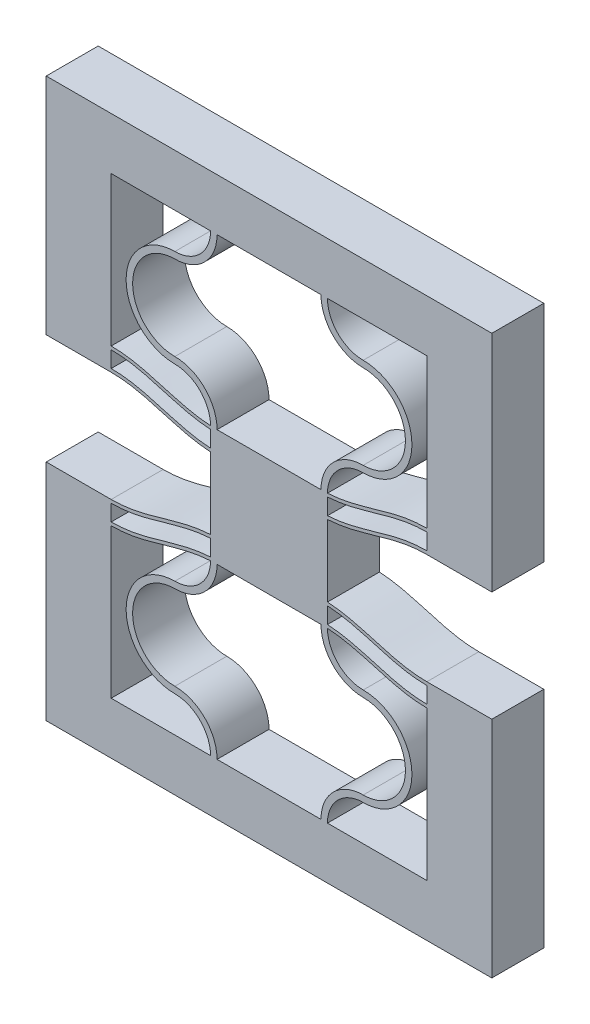
SolidWorks part; units mm, degrees
ref_plane "Front Plane" through (0, 0, 0) normal (0, 0, 1) x (1, 0, 0)
ref_plane "Top Plane" through (0, 0, 0) normal (0, 1, 0) x (1, 0, 0)
ref_plane "Right Plane" through (0, 0, 0) normal (1, 0, 0) x (0, 0, -1)
sketch "Sketch1" plane through (0, 0, 0) normal (0, 0, 1) x (1, 0, 0)
  line L4 (0, 11.5) -> (0, 0)
  line L5 (8.15, 0) -> (8.15, 13) construction
  line L6 (8.15, 13) -> (8.15, 15.9894) construction
  line L17 (7.65, 0) -> (0, 0)
  line L18 (8.65, 0) -> (16.3, 0)
  line L19 (16.3, 0) -> (16.3, 11.5)
  line L20 (8.65, 13.2361) -> (8.65, 14.4861)
  line L21 (7.65, 13.2361) -> (7.65, 14.4861)
  line L22 (8.65, 15.9894) -> (8.65, 14.7361)
  line L23 (8.65, 15.9894) -> (7.65, 15.9894)
  line L24 (7.65, 15.9894) -> (7.65, 14.7361)
  line L31 (-4.9999, 13.25) -> (-4.9999, -4)
  line L32 (-4.9999, -4) -> (21.2999, -4)
  line L33 (21.2999, -4) -> (21.2999, 13.25)
  line L34 (0, 11.75) -> (0, 13)
  line L36 (-4.9999, 13.25) -> (0, 13.25)
  line L37 (21.2999, 13.25) -> (16.3, 13.25)
  line L38 (16.3, 11.75) -> (16.3, 13)
  arc A0 (8.15, 13) -> (4.9, 9.75) centre (4.9, 13) cw
  arc A1 (4.9, 9.75) -> (4.9, 3.25) centre (4.9, 6.5) ccw
  arc A2 (4.9, 3.25) -> (8.15, 0) centre (4.9, 0) cw
  arc A3 (7.65, 12.9861) -> (4.9, 10.25) centre (4.9, 13) cw
  arc A4 (4.9, 10.25) -> (4.9, 2.75) centre (4.9, 6.5) ccw
  arc A5 (4.9, 2.75) -> (7.65, 0) centre (4.9, 0) cw
  arc A6 (7.65, 13) -> (4.9, 10.25) centre (4.9, 13) cw construction
  arc A7 (11.4, 3.25) -> (8.15, 0) centre (11.4, 0) ccw
  arc A8 (11.4, 2.75) -> (8.65, 0) centre (11.4, 0) ccw
  arc A9 (11.4, 9.75) -> (11.4, 3.25) centre (11.4, 6.5) cw
  arc A10 (11.4, 10.25) -> (11.4, 2.75) centre (11.4, 6.5) cw
  arc A11 (8.65, 12.9861) -> (11.4, 10.25) centre (11.4, 13) ccw
  arc A12 (8.15, 13) -> (11.4, 9.75) centre (11.4, 13) ccw
  spline S0 degree 4 poles (-1.6301, 11.6432) (-1.58, 11.6346) (-1.4751, 11.618) (-1.3291, 11.5948) (-1.1153, 11.568) (-0.875, 11.5398) (-0.5953, 11.5188) (-0.3803, 11.5054) (-0.0328, 11.499) (0.0886, 11.4999) (0.3795, 11.5059) (0.5682, 11.518) (0.8277, 11.5353) (1.0822, 11.563) (1.4006, 11.6043) (1.7549, 11.663) (2.1668, 11.7432) (2.6464, 11.8542) (3.2011, 11.9994) (3.9255, 12.2053) (4.7738, 12.4548) (5.6271, 12.6855) (6.4939, 12.863) (7.2157, 12.9603) (7.8381, 13.0036) (8.4619, 13.0036) (9.0842, 12.9603) (9.8062, 12.863) (10.6728, 12.6855) (11.5263, 12.4548) (12.3744, 12.2053) (13.0365, 12.0172) (13.464, 11.9038) (13.8677, 11.8046) (14.1995, 11.7307) (14.5418, 11.6629) (14.9045, 11.6043) (15.1694, 11.5682) (15.411, 11.5432) (15.59, 11.5266) (15.7731, 11.5159) (15.9135, 11.5059) (16.2148, 11.4999) (16.3292, 11.499) (16.626, 11.5042) (16.7956, 11.5134) (16.9939, 11.5254) (17.136, 11.5385) (17.2944, 11.5538) (17.4445, 11.5713) (17.6002, 11.5915) (17.7516, 11.6141) (17.8539, 11.6304) (17.9047, 11.6389) (17.93, 11.6432) knots 0 0 0 0 0 0.010347 0.020694 0.031041 0.041388 0.061831 0.072053 0.082275 0.097927 0.105753 0.113579 0.129231 0.144883 0.160535 0.176188 0.202358 0.228529 0.259833 0.291137 0.353746 0.406087 0.437391 0.468696 0.5 0.531304 0.562609 0.593913 0.646254 0.708863 0.740167 0.771471 0.784557 0.797642 0.823812 0.839465 0.855117 0.870769 0.878595 0.886421 0.894247 0.902073 0.917725 0.927947 0.938169 0.94839 0.958612 0.963785 0.968959 0.979306 0.989653 0.994826 1 1 1 1 1 construction
  spline S1 degree 4 poles (0, 11.5) (0.0651, 11.5) (0.1602, 11.5014) (0.3795, 11.5059) (0.5682, 11.518) (0.8277, 11.5353) (1.0822, 11.563) (1.4006, 11.6043) (1.7549, 11.663) (2.1668, 11.7432) (2.6464, 11.8542) (3.2011, 11.9994) (3.9255, 12.2053) (4.7738, 12.4548) (5.6271, 12.6855) (6.4939, 12.863) (7.2157, 12.9603) (7.8381, 13.0036) (8.4619, 13.0036) (9.0842, 12.9603) (9.8062, 12.863) (10.6728, 12.6855) (11.5263, 12.4548) (12.3744, 12.2053) (13.0365, 12.0172) (13.464, 11.9038) (13.8677, 11.8046) (14.1995, 11.7307) (14.5418, 11.6629) (14.9045, 11.6043) (15.1694, 11.5682) (15.411, 11.5432) (15.59, 11.5266) (15.7731, 11.5159) (15.9135, 11.5059) (16.1407, 11.5014) (16.2349, 11.5) (16.3, 11.5) knots 0.082275 0.082275 0.082275 0.082275 0.082275 0.097927 0.105753 0.113579 0.129231 0.144883 0.160535 0.176188 0.202358 0.228529 0.259833 0.291137 0.353746 0.406087 0.437391 0.468696 0.5 0.531304 0.562609 0.593913 0.646254 0.708863 0.740167 0.771471 0.784557 0.797642 0.823812 0.839465 0.855117 0.870769 0.878595 0.886421 0.894247 0.902073 0.917725 0.917725 0.917725 0.917725 0.917725
  spline S2 degree 4 poles (-1.6301, 11.8932) (-1.58, 11.8846) (-1.4751, 11.868) (-1.3291, 11.8448) (-1.1153, 11.818) (-0.875, 11.7898) (-0.5953, 11.7688) (-0.3803, 11.7554) (-0.0328, 11.749) (0.0886, 11.7499) (0.3795, 11.7559) (0.5682, 11.768) (0.8277, 11.7853) (1.0822, 11.813) (1.4006, 11.8543) (1.7549, 11.913) (2.1668, 11.9932) (2.6464, 12.1042) (3.2011, 12.2494) (3.9255, 12.4553) (4.7738, 12.7048) (5.6271, 12.9355) (6.4939, 13.113) (7.2157, 13.2103) (7.8381, 13.2536) (8.4619, 13.2536) (9.0842, 13.2103) (9.8062, 13.113) (10.6728, 12.9355) (11.5263, 12.7048) (12.3744, 12.4553) (13.0365, 12.2672) (13.464, 12.1538) (13.8677, 12.0546) (14.1995, 11.9807) (14.5418, 11.9129) (14.9045, 11.8543) (15.1694, 11.8182) (15.411, 11.7932) (15.59, 11.7766) (15.7731, 11.7659) (15.9135, 11.7559) (16.2148, 11.7499) (16.3292, 11.749) (16.626, 11.7542) (16.7956, 11.7634) (16.9939, 11.7754) (17.136, 11.7885) (17.2944, 11.8038) (17.4445, 11.8213) (17.6002, 11.8415) (17.7516, 11.8641) (17.8539, 11.8804) (17.9047, 11.8889) (17.93, 11.8932) knots 0 0 0 0 0 0.010347 0.020694 0.031041 0.041388 0.061831 0.072053 0.082275 0.097927 0.105753 0.113579 0.129231 0.144883 0.160535 0.176188 0.202358 0.228529 0.259833 0.291137 0.353746 0.406087 0.437391 0.468696 0.5 0.531304 0.562609 0.593913 0.646254 0.708863 0.740167 0.771471 0.784557 0.797642 0.823812 0.839465 0.855117 0.870769 0.878595 0.886421 0.894247 0.902073 0.917725 0.927947 0.938169 0.94839 0.958612 0.963785 0.968959 0.979306 0.989653 0.994826 1 1 1 1 1 construction
  spline S3 degree 4 poles (0, 11.75) (0.0651, 11.75) (0.1602, 11.7514) (0.3795, 11.7559) (0.5682, 11.768) (0.8277, 11.7853) (1.0822, 11.813) (1.4006, 11.8543) (1.7549, 11.913) (2.1668, 11.9932) (2.6464, 12.1042) (3.2011, 12.2494) (3.9255, 12.4553) (4.7738, 12.7048) (5.6271, 12.9355) (6.4939, 13.113) (7.2157, 13.2103) (7.8381, 13.2536) (8.4619, 13.2536) (9.0842, 13.2103) (9.8062, 13.113) (10.6728, 12.9355) (11.5263, 12.7048) (12.3744, 12.4553) (13.0365, 12.2672) (13.464, 12.1538) (13.8677, 12.0546) (14.1995, 11.9807) (14.5418, 11.9129) (14.9045, 11.8543) (15.1694, 11.8182) (15.411, 11.7932) (15.59, 11.7766) (15.7731, 11.7659) (15.9135, 11.7559) (16.1407, 11.7514) (16.2349, 11.75) (16.3, 11.75) knots 0.082275 0.082275 0.082275 0.082275 0.082275 0.097927 0.105753 0.113579 0.129231 0.144883 0.160535 0.176188 0.202358 0.228529 0.259833 0.291137 0.353746 0.406087 0.437391 0.468696 0.5 0.531304 0.562609 0.593913 0.646254 0.708863 0.740167 0.771471 0.784557 0.797642 0.823812 0.839465 0.855117 0.870769 0.878595 0.886421 0.894247 0.902073 0.917725 0.917725 0.917725 0.917725 0.917725
  spline S4 degree 4 poles (-1.6301, 13.1432) (-1.58, 13.1346) (-1.4751, 13.118) (-1.3291, 13.0948) (-1.1153, 13.068) (-0.875, 13.0398) (-0.5953, 13.0188) (-0.3803, 13.0054) (-0.0328, 12.999) (0.0886, 12.9999) (0.3795, 13.0059) (0.5682, 13.018) (0.8277, 13.0353) (1.0822, 13.063) (1.4006, 13.1043) (1.7549, 13.163) (2.1668, 13.2432) (2.6464, 13.3542) (3.2011, 13.4994) (3.9255, 13.7053) (4.7738, 13.9548) (5.6271, 14.1855) (6.4939, 14.363) (7.2157, 14.4603) (7.8381, 14.5036) (8.4619, 14.5036) (9.0842, 14.4603) (9.8062, 14.363) (10.6728, 14.1855) (11.5263, 13.9548) (12.3744, 13.7053) (13.0365, 13.5172) (13.464, 13.4038) (13.8677, 13.3046) (14.1995, 13.2307) (14.5418, 13.1629) (14.9045, 13.1043) (15.1694, 13.0682) (15.411, 13.0432) (15.59, 13.0266) (15.7731, 13.0159) (15.9135, 13.0059) (16.2148, 12.9999) (16.3292, 12.999) (16.626, 13.0042) (16.7956, 13.0134) (16.9939, 13.0254) (17.136, 13.0385) (17.2944, 13.0538) (17.4445, 13.0713) (17.6002, 13.0915) (17.7516, 13.1141) (17.8539, 13.1304) (17.9047, 13.1389) (17.93, 13.1432) knots 0 0 0 0 0 0.010347 0.020694 0.031041 0.041388 0.061831 0.072053 0.082275 0.097927 0.105753 0.113579 0.129231 0.144883 0.160535 0.176188 0.202358 0.228529 0.259833 0.291137 0.353746 0.406087 0.437391 0.468696 0.5 0.531304 0.562609 0.593913 0.646254 0.708863 0.740167 0.771471 0.784557 0.797642 0.823812 0.839465 0.855117 0.870769 0.878595 0.886421 0.894247 0.902073 0.917725 0.927947 0.938169 0.94839 0.958612 0.963785 0.968959 0.979306 0.989653 0.994826 1 1 1 1 1 construction
  spline S5 degree 4 poles (0, 13) (0.0651, 13) (0.1602, 13.0014) (0.3795, 13.0059) (0.5682, 13.018) (0.8277, 13.0353) (1.0822, 13.063) (1.4006, 13.1043) (1.7549, 13.163) (2.1668, 13.2432) (2.6464, 13.3542) (3.2011, 13.4994) (3.9255, 13.7053) (4.7738, 13.9548) (5.6271, 14.1855) (6.4939, 14.363) (7.2157, 14.4603) (7.8381, 14.5036) (8.4619, 14.5036) (9.0842, 14.4603) (9.8062, 14.363) (10.6728, 14.1855) (11.5263, 13.9548) (12.3744, 13.7053) (13.0365, 13.5172) (13.464, 13.4038) (13.8677, 13.3046) (14.1995, 13.2307) (14.5418, 13.1629) (14.9045, 13.1043) (15.1694, 13.0682) (15.411, 13.0432) (15.59, 13.0266) (15.7731, 13.0159) (15.9135, 13.0059) (16.1407, 13.0014) (16.2349, 13) (16.3, 13) knots 0.082275 0.082275 0.082275 0.082275 0.082275 0.097927 0.105753 0.113579 0.129231 0.144883 0.160535 0.176188 0.202358 0.228529 0.259833 0.291137 0.353746 0.406087 0.437391 0.468696 0.5 0.531304 0.562609 0.593913 0.646254 0.708863 0.740167 0.771471 0.784557 0.797642 0.823812 0.839465 0.855117 0.870769 0.878595 0.886421 0.894247 0.902073 0.917725 0.917725 0.917725 0.917725 0.917725
  spline S6 degree 4 poles (-1.6301, 13.3932) (-1.58, 13.3846) (-1.4751, 13.368) (-1.3291, 13.3448) (-1.1153, 13.318) (-0.875, 13.2898) (-0.5953, 13.2688) (-0.3803, 13.2554) (-0.0328, 13.249) (0.0886, 13.2499) (0.3795, 13.2559) (0.5682, 13.268) (0.8277, 13.2853) (1.0822, 13.313) (1.4006, 13.3543) (1.7549, 13.413) (2.1668, 13.4932) (2.6464, 13.6042) (3.2011, 13.7494) (3.9255, 13.9553) (4.7738, 14.2048) (5.6271, 14.4355) (6.4939, 14.613) (7.2157, 14.7103) (7.8381, 14.7536) (8.4619, 14.7536) (9.0842, 14.7103) (9.8062, 14.613) (10.6728, 14.4355) (11.5263, 14.2048) (12.3744, 13.9553) (13.0365, 13.7672) (13.464, 13.6538) (13.8677, 13.5546) (14.1995, 13.4807) (14.5418, 13.4129) (14.9045, 13.3543) (15.1694, 13.3182) (15.411, 13.2932) (15.59, 13.2766) (15.7731, 13.2659) (15.9135, 13.2559) (16.2148, 13.2499) (16.3292, 13.249) (16.626, 13.2542) (16.7956, 13.2634) (16.9939, 13.2754) (17.136, 13.2885) (17.2944, 13.3038) (17.4445, 13.3213) (17.6002, 13.3415) (17.7516, 13.3641) (17.8539, 13.3804) (17.9047, 13.3889) (17.93, 13.3932) knots 0 0 0 0 0 0.010347 0.020694 0.031041 0.041388 0.061831 0.072053 0.082275 0.097927 0.105753 0.113579 0.129231 0.144883 0.160535 0.176188 0.202358 0.228529 0.259833 0.291137 0.353746 0.406087 0.437391 0.468696 0.5 0.531304 0.562609 0.593913 0.646254 0.708863 0.740167 0.771471 0.784557 0.797642 0.823812 0.839465 0.855117 0.870769 0.878595 0.886421 0.894247 0.902073 0.917725 0.927947 0.938169 0.94839 0.958612 0.963785 0.968959 0.979306 0.989653 0.994826 1 1 1 1 1 construction
  spline S7 degree 4 poles (0, 13.25) (0.0651, 13.25) (0.1602, 13.2514) (0.3795, 13.2559) (0.5682, 13.268) (0.8277, 13.2853) (1.0822, 13.313) (1.4006, 13.3543) (1.7549, 13.413) (2.1668, 13.4932) (2.6464, 13.6042) (3.2011, 13.7494) (3.9255, 13.9553) (4.7738, 14.2048) (5.6271, 14.4355) (6.4939, 14.613) (7.2157, 14.7103) (7.8381, 14.7536) (8.4619, 14.7536) (9.0842, 14.7103) (9.8062, 14.613) (10.6728, 14.4355) (11.5263, 14.2048) (12.3744, 13.9553) (13.0365, 13.7672) (13.464, 13.6538) (13.8677, 13.5546) (14.1995, 13.4807) (14.5418, 13.4129) (14.9045, 13.3543) (15.1694, 13.3182) (15.411, 13.2932) (15.59, 13.2766) (15.7731, 13.2659) (15.9135, 13.2559) (16.1407, 13.2514) (16.2349, 13.25) (16.3, 13.25) knots 0.082275 0.082275 0.082275 0.082275 0.082275 0.097927 0.105753 0.113579 0.129231 0.144883 0.160535 0.176188 0.202358 0.228529 0.259833 0.291137 0.353746 0.406087 0.437391 0.468696 0.5 0.531304 0.562609 0.593913 0.646254 0.708863 0.740167 0.771471 0.784557 0.797642 0.823812 0.839465 0.855117 0.870769 0.878595 0.886421 0.894247 0.902073 0.917725 0.917725 0.917725 0.917725 0.917725
  point P5 (8.65, 15.9894)
  dimension "D4" = 0.25
  dimension "D6" = 4
  dimension "D1" = 13
  dimension "D2" = 0.5
  dimension "D3" = 0.25
  dimension "D7" = 4.9999
  dimension "D5" = 1.5
extrude "Boss-Extrude1" add sketch "Sketch1" along normal blind 4
sketch "Sketch4" plane through (0, 15.9894, 0) normal (0, 1, 0) x (1, 0, 0)
  line L24 (8.65, 0) -> (7.65, 0)
  line L25 (7.65, 0) -> (7.65, -4)
  line L26 (8.65, 0) -> (7.65, 0)
  line L27 (8.65, -4) -> (8.65, 0)
  line L29 (7.65, 0) -> (7.65, -4)
  line L32 (7.65, -4) -> (8.65, -4)
  line L33 (7.65, -4) -> (8.65, -4)
  line L34 (8.65, -4) -> (8.65, 0)
  dimension "D1" = 0
extrude "Boss-Extrude2" add sketch "Sketch4" along normal blind 1.5
mirror "Mirror3" about plane through (0, 17.4894, 0) normal (0, 1, 0) of bodies 179
ref_plane "Plane1" through (8.15, 0, 0) normal (-1, 0, 0) x (0, 0, 1)
split "Split2" trim tools "Plane1" bodies to split 247 102 resulting bodies 225
sketch "Sketch7" plane through (8.15, 0, 0) normal (-1, 0, 0) x (0, 0, 1)
  line L4 (4, 34.9787) -> (4, 38.9787)
  line L12 (0, 13) -> (4, 13)
  line L13 (0, 13) -> (4, 13)
  line L14 (4, 13) -> (4, 21.9787)
  line L15 (4, 13) -> (4, 21.9787)
  line L20 (4, 0) -> (0, 0)
  line L22 (4, 0) -> (0, 0)
  line L23 (0, -4) -> (4, -4)
  line L27 (0, -4) -> (4, -4)
  line L31 (4, 21.9787) -> (0, 21.9787)
  line L32 (4, 21.9787) -> (0, 21.9787)
  line L33 (0, 21.9787) -> (0, 13)
  line L34 (0, 21.9787) -> (0, 13)
  line L36 (4, -4) -> (4, 0)
  line L38 (4, 34.9787) -> (4, 38.9787)
  line L39 (4, 34.9787) -> (4, 38.9787)
  line L40 (4, 38.9787) -> (0, 38.9787)
  line L41 (4, 38.9787) -> (0, 38.9787)
  line L46 (4, 34.9787) -> (4, 38.9787)
  line L51 (0, 38.9787) -> (0, 34.9787)
  line L52 (0, 38.9787) -> (0, 34.9787)
  line L53 (0, 34.9787) -> (4, 34.9787)
  line L54 (0, 34.9787) -> (4, 34.9787)
  line L55 (4, 38.9787) -> (0, 38.9787)
  line L57 (4, 38.9787) -> (0, 38.9787)
  line L59 (4, -4) -> (4, 0)
  line L60 (0, 0) -> (0, -4)
  line L61 (0, 0) -> (0, -4)
  line L62 (0, 38.9787) -> (0, 34.9787)
  line L63 (0, 38.9787) -> (0, 34.9787)
  line L64 (0, 34.9787) -> (4, 34.9787)
  line L65 (0, 34.9787) -> (4, 34.9787)
  dimension "D1" = 0
  dimension "D2" = 0
  dimension "D3" = 0
  dimension "D4" = 0
extrude "Boss-Extrude3" add sketch "Sketch7" along normal blind 4
mirror "Mirror2" about plane through (4.15, 0, 0) normal (-1, 0, 0) of bodies 226
